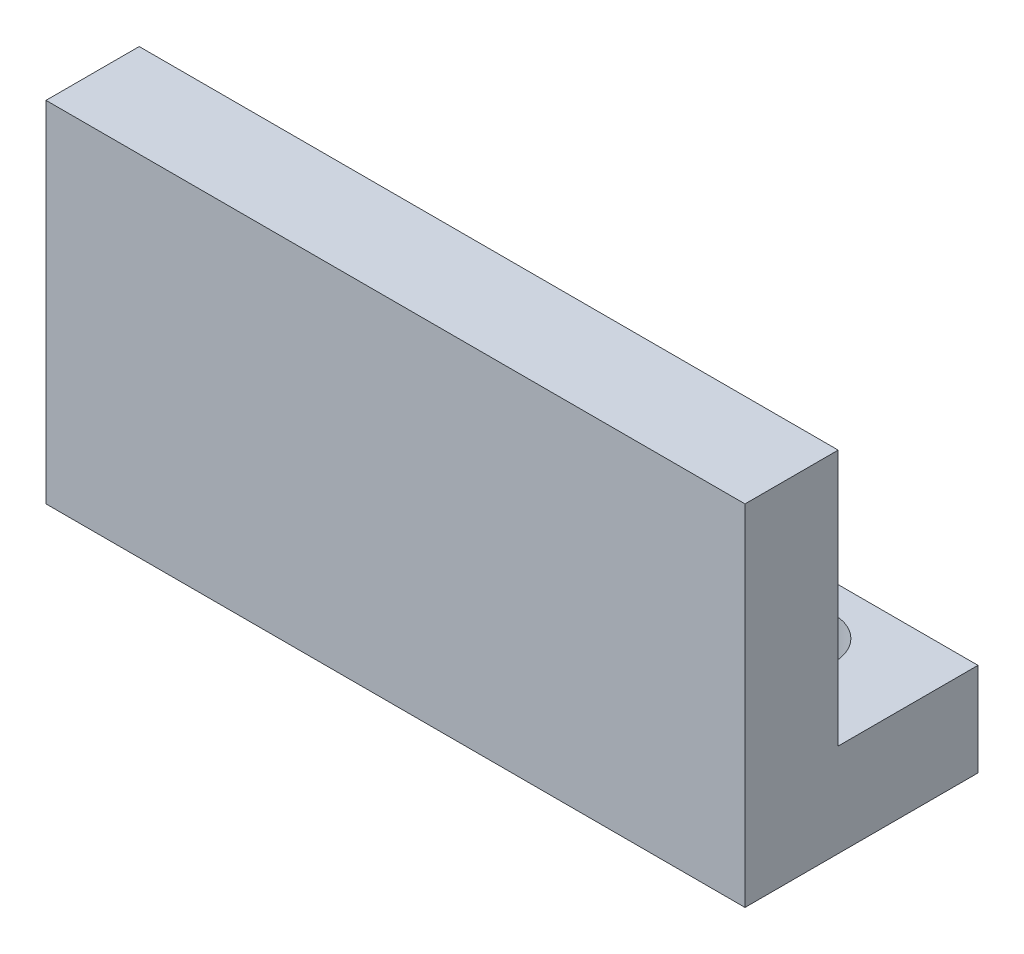
SolidWorks part; units mm, degrees
ref_plane "Front Plane" through (0, 0, 0) normal (0, 0, 1) x (1, 0, 0)
ref_plane "Top Plane" through (0, 0, 0) normal (0, 1, 0) x (1, 0, 0)
ref_plane "Right Plane" through (0, 0, 0) normal (1, 0, 0) x (0, 0, -1)
sketch "Sketch1" plane through (0, 0, 0) normal (1, 0, 0) x (0, 0, -1)
  line L0 (0, 15) -> (0, 0)
  line L1 (0, 0) -> (10, 0)
  line L2 (10, 0) -> (10, 4)
  line L3 (10, 4) -> (4, 4)
  line L4 (4, 4) -> (4, 15)
  line L5 (0, 15) -> (4, 15)
  point P4 (0, 7.5)
  point P8 (10, 2)
  dimension "D1" = 10
  dimension "D2" = 15
  dimension "D3" = 4
  dimension "D4" = 4
extrude "Boss-Extrude1" add sketch "Sketch1" along normal blind 30
hole_wizard "M3 Clearance Hole1" positions "Sketch2" profile "Sketch3" hole size "M3" standard "ANSI Metric" end condition through all
sketch "Sketch2" plane through (0, 4, 0) normal (0, 1, 0) x (1, 0, 0)
  line L0 (0, 10) -> (0, 4) construction
  line L1 (30, 10) -> (30, 4) construction
  line L2 (30, 10) -> (0, 10) construction
  point P0 (5, 7)
  point P2 (25, 7)
  point P9 (30, 7)
  point P10 (5, 7.3923)
  dimension "D1" = 20
  dimension "D2" = 5
  dimension "D3" = 5
  dimension "D4" = 3
sketch "Sketch3" plane through (5, 4, -7) normal (1, 0, 0) x (0, 0, 1)
  line L0 (0, 0) -> (0, 4)
  line L1 (0, 4) -> (1.8, 4)
  line L2 (1.8, 4) -> (1.8, 0)
  line L5 (1.8, 0) -> (0, 0)
  line L11 (0, -6.35) -> (0, 107.95) construction
  dimension "Thru Hole Dia." = 3.6
  dimension "Thru Hole Depth" = 4
